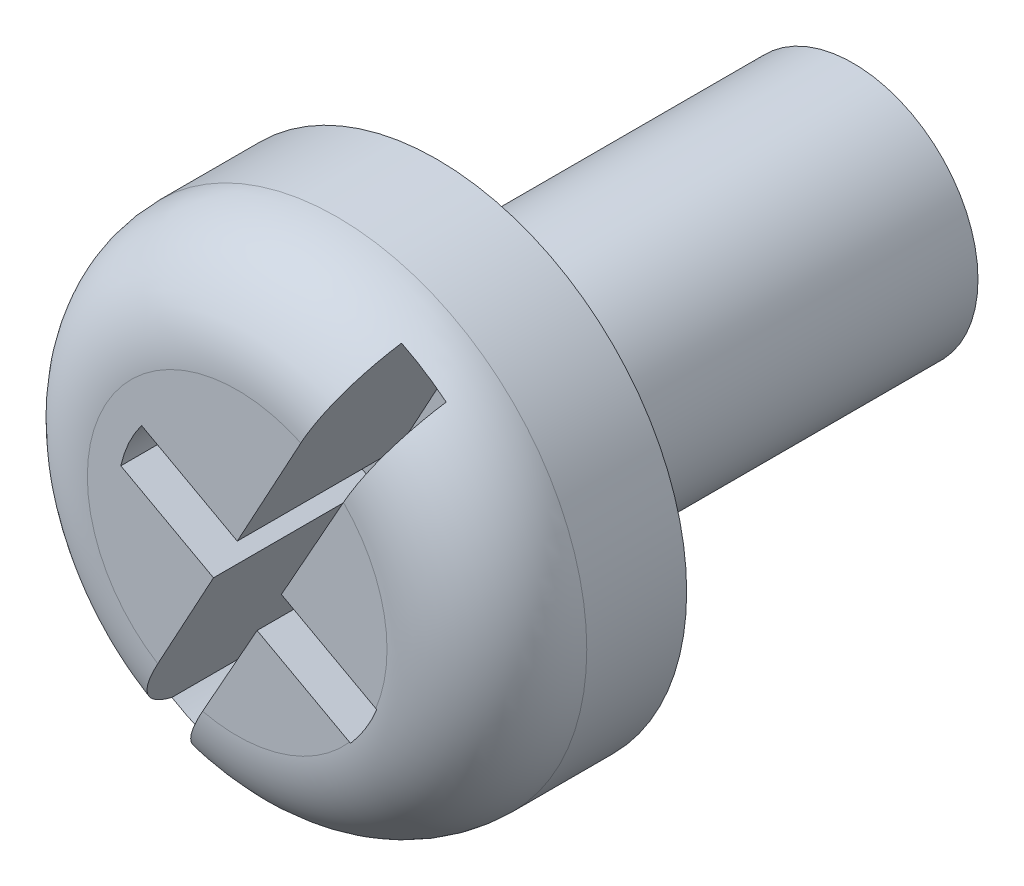
SolidWorks part; units mm, degrees
material "Stop odlewniczy stali"
ref_plane "Płaszczyzna przednia" through (0, 0, 0) normal (0, 0, 1) x (1, 0, 0)
ref_plane "Płaszczyzna górna" through (0, 0, 0) normal (0, 1, 0) x (1, 0, 0)
ref_plane "Płaszczyzna prawa" through (0, 0, 0) normal (1, 0, 0) x (0, 0, -1)
sketch "Szkic1" plane through (0, 0, 0) normal (0, 0, 1) x (1, 0, 0)
  circle A0 centre (-1.8605, 2.7321) radius 3
  dimension "D1" = 6
extrude "Dodanie-wyciągnięcie2" add sketch "Szkic1" along normal blind 2.4
sketch "Szkic2" plane through (0, 0, 0) normal (0, 0, -1) x (-1, 0, 0)
  circle A0 centre (1.8605, 2.7321) radius 1.5
extrude "Dodanie-wyciągnięcie3" add sketch "Szkic2" along normal blind 5
fillet "Zaokrąglenie2" radius 1.2 1 edges at (1.1395, 2.7321, 2.4)
sketch "Szkic3" plane through (0, 0, 2.4) normal (0, 0, 1) x (1, 0, 0)
  line L0 (-1.8595, 2.9591) -> (-0.5756, 5.3165)
  line L1 (-1.8595, 2.9591) -> (-3.0095, 3.5874)
  line L2 (-3.3345, 0.2508) -> (-2.1451, 2.4347)
  line L3 (-2.8199, 0.0102) -> (-1.6213, 2.1486)
  line L4 (-0.184, 2.0436) -> (-1.3294, 2.6694)
  line L5 (-0.4992, 1.5357) -> (-1.6213, 2.1486)
  line L6 (-1.3294, 2.6694) -> (-0.0393, 4.9711)
  line L7 (-2.1451, 2.4347) -> (-3.2587, 3.0429)
  arc A2 (-3.0095, 3.5874) -> (-3.2587, 3.0429) centre (-1.8605, 2.7321) ccw
  arc A3 (-0.0393, 4.9711) -> (-0.5756, 5.3165) centre (-1.8605, 2.7321) ccw
  arc A4 (-3.3345, 0.2508) -> (-2.8199, 0.0102) centre (-1.8605, 2.7321) ccw
  arc A6 (-0.4992, 1.5357) -> (-0.184, 2.0436) centre (-1.8605, 2.7321) ccw
extrude "Wytnij-wyciągnięcie1" cut sketch "Szkic3" against normal blind 1.94
